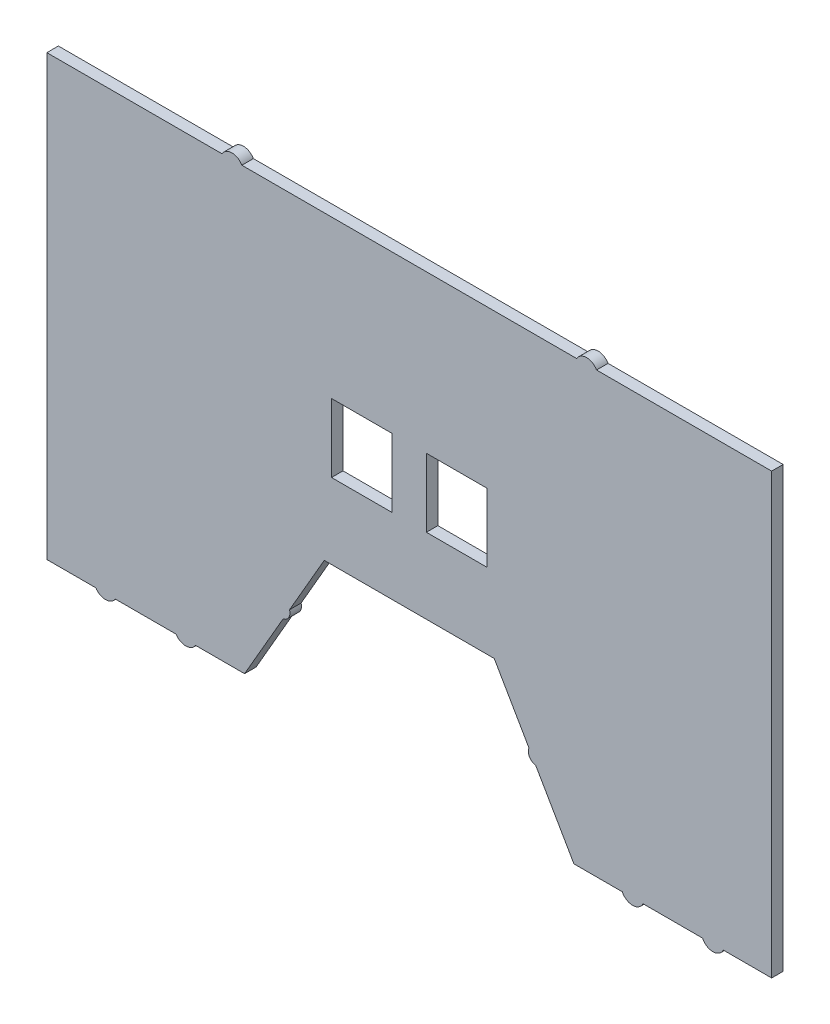
SolidWorks part; units mm, degrees
ref_plane "Front Plane" through (0, 0, 0) normal (0, 0, 1) x (1, 0, 0)
ref_plane "Top Plane" through (0, 0, 0) normal (0, 1, 0) x (1, 0, 0)
ref_plane "Right Plane" through (0, 0, 0) normal (1, 0, 0) x (0, 0, -1)
sketch "Sketch1" plane through (0, 0, 0) normal (0, 0, 1) x (1, 0, 0)
  line L25 (-39.7254, 27.1353) -> (-13.3666, 27.1353)
  line L26 (-39.7254, 27.1353) -> (-39.7254, -2.6246)
  line L27 (-39.7254, -2.6246) -> (-13.3666, -2.6246)
  line L28 (-13.3666, 27.1353) -> (-13.3666, -2.6246)
  line L29 (-39.7254, 27.1353) -> (-13.3666, -2.6246) construction
  line L30 (-39.7254, -2.6246) -> (-13.3666, 27.1353) construction
  line L31 (1.5288, 27.1353) -> (27.8875, 27.1353)
  line L32 (1.5288, 27.1353) -> (1.5288, -2.6246)
  line L33 (1.5288, -2.6246) -> (27.8875, -2.6246)
  line L34 (27.8875, 27.1353) -> (27.8875, -2.6246)
  line L35 (1.5288, 27.1353) -> (27.8875, -2.6246) construction
  line L36 (1.5288, -2.6246) -> (27.8875, 27.1353) construction
  line L40 (-133.7057, -95.388) -> (-107.275, -95.388)
  line L41 (-98.8146, -95.388) -> (-77.5104, -95.388)
  line L42 (-77.5104, -95.388) -> (-60.7651, -66.3842)
  line L43 (-57.97, -61.543) -> (-42.8694, -35.388)
  line L44 (-42.8694, -35.388) -> (31.0314, -35.388)
  line L45 (31.0314, -35.388) -> (46.1208, -61.5237)
  line L46 (49.068, -66.6284) -> (65.6724, -95.388)
  line L47 (65.6724, -95.388) -> (86.6859, -95.388)
  line L48 (95.7261, -95.388) -> (121.5786, -95.388)
  line L49 (130.6189, -95.388) -> (151.6323, -95.388)
  line L50 (151.6323, -95.388) -> (151.6323, 95.4654)
  line L51 (151.6323, 95.4654) -> (75.5122, 95.4654)
  line L52 (66.8519, 95.4654) -> (-78.6898, 95.4654)
  line L53 (-87.35, 95.4654) -> (-163.4703, 95.4654)
  line L54 (-163.4703, 95.4654) -> (-163.4703, -95.388)
  line L55 (-163.4703, -95.388) -> (-142.1661, -95.388)
  line L56 (-133.7057, -95.388) -> (-107.275, -95.388)
  line L57 (-98.8146, -95.388) -> (-77.5104, -95.388)
  line L58 (-77.5104, -95.388) -> (-60.7651, -66.3842)
  line L59 (-57.97, -61.543) -> (-42.8694, -35.388)
  line L60 (-42.8694, -35.388) -> (31.0314, -35.388)
  line L61 (31.0314, -35.388) -> (46.1208, -61.5237)
  line L62 (49.068, -66.6284) -> (65.6724, -95.388)
  line L63 (65.6724, -95.388) -> (86.6859, -95.388)
  line L64 (95.7261, -95.388) -> (121.5786, -95.388)
  line L65 (130.6189, -95.388) -> (151.6323, -95.388)
  line L66 (151.6323, -95.388) -> (151.6323, 95.4654)
  line L67 (151.6323, 95.4654) -> (75.5122, 95.4654)
  line L68 (66.8519, 95.4654) -> (-78.6898, 95.4654)
  line L69 (-87.35, 95.4654) -> (-163.4703, 95.4654)
  line L70 (-163.4703, 95.4654) -> (-163.4703, -95.388)
  line L71 (-163.4703, -95.388) -> (-142.1661, -95.388)
  arc A12 (-142.1661, -95.388) -> (-133.7057, -95.388) centre (-137.9359, -92.7224) ccw
  arc A13 (-107.275, -95.388) -> (-98.8146, -95.388) centre (-103.0448, -92.7224) ccw
  arc A14 (-60.7651, -66.3842) -> (-57.97, -61.543) centre (-61.5326, -62.7136) ccw
  arc A15 (46.1208, -61.5237) -> (49.068, -66.6284) centre (49.6025, -62.9167) ccw
  arc A16 (86.6859, -95.388) -> (95.7261, -95.388) centre (91.206, -93.2506) ccw
  arc A17 (121.5786, -95.388) -> (130.6189, -95.388) centre (126.0987, -93.2506) ccw
  arc A18 (75.5122, 95.4654) -> (66.8519, 95.4654) centre (71.182, 92.9654) ccw
  arc A19 (-78.6898, 95.4654) -> (-87.35, 95.4654) centre (-83.0199, 92.9654) ccw
  arc A20 (-142.1661, -95.388) -> (-133.7057, -95.388) centre (-137.9359, -92.7224) ccw
  arc A21 (-107.275, -95.388) -> (-98.8146, -95.388) centre (-103.0448, -92.7224) ccw
  arc A22 (-60.7651, -66.3842) -> (-57.97, -61.543) centre (-61.5326, -62.7136) ccw
  arc A23 (46.1208, -61.5237) -> (49.068, -66.6284) centre (49.6025, -62.9167) ccw
  arc A24 (86.6859, -95.388) -> (95.7261, -95.388) centre (91.206, -93.2506) ccw
  arc A25 (121.5786, -95.388) -> (130.6189, -95.388) centre (126.0987, -93.2506) ccw
  arc A26 (75.5122, 95.4654) -> (66.8519, 95.4654) centre (71.182, 92.9654) ccw
  arc A27 (-78.6898, 95.4654) -> (-87.35, 95.4654) centre (-83.0199, 92.9654) ccw
  point P22 (-26.546, 12.2554)
  point P31 (14.7081, 12.2554)
  dimension "D1" = 0
extrude "Boss-Extrude1" add sketch "Sketch1" along normal blind 5
